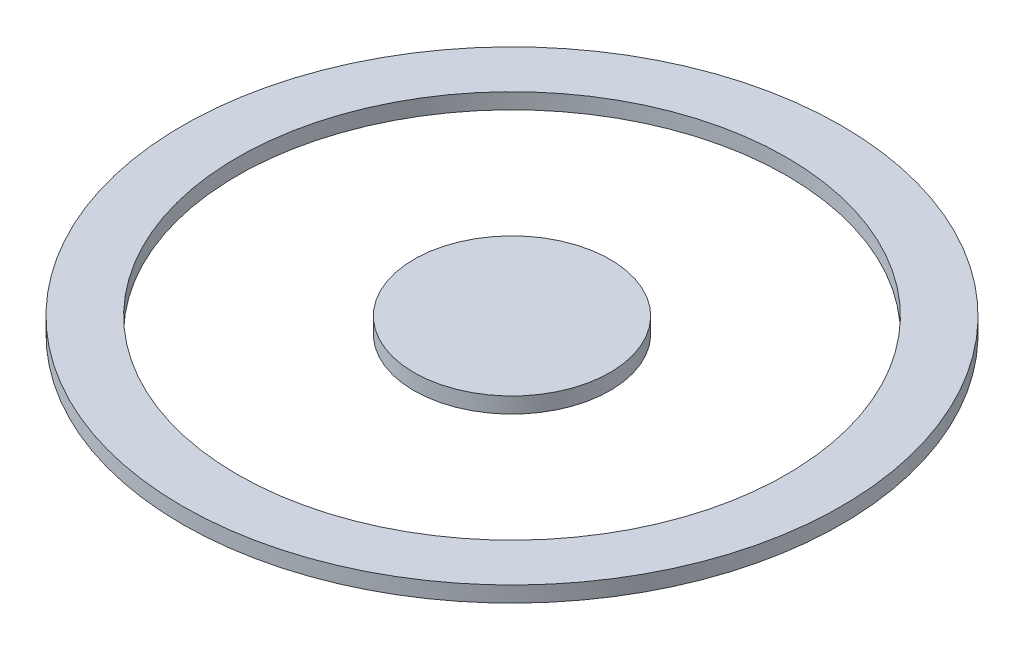
SolidWorks part; units mm, degrees
material "Perspex (TM) GS Acrylic Cast Sheet"
ref_plane "Front Plane" through (0, 0, 0) normal (0, 0, 1) x (1, 0, 0)
ref_plane "Top Plane" through (0, 0, 0) normal (0, 1, 0) x (1, 0, 0)
ref_plane "Right Plane" through (0, 0, 0) normal (1, 0, 0) x (0, 0, -1)
sketch "Sketch1" plane through (0, 0, 0) normal (0, 1, 0) x (1, 0, 0)
  circle A0 centre (0, 0) radius 42
  dimension "D1" = 84
extrude "Boss-Extrude1" add sketch "Sketch1" along normal blind 2
sketch "Sketch2" plane through (0, 2, 0) normal (0, 1, 0) x (1, 0, 0)
  circle A0 centre (0, 0) radius 35
  circle A1 centre (0, 0) radius 12.5
  circle A2 centre (0, 0) radius 42 construction
  dimension "D1" = 7
  dimension "D2" = 25
extrude "Cut-Extrude1" cut sketch "Sketch2" against normal blind 2
